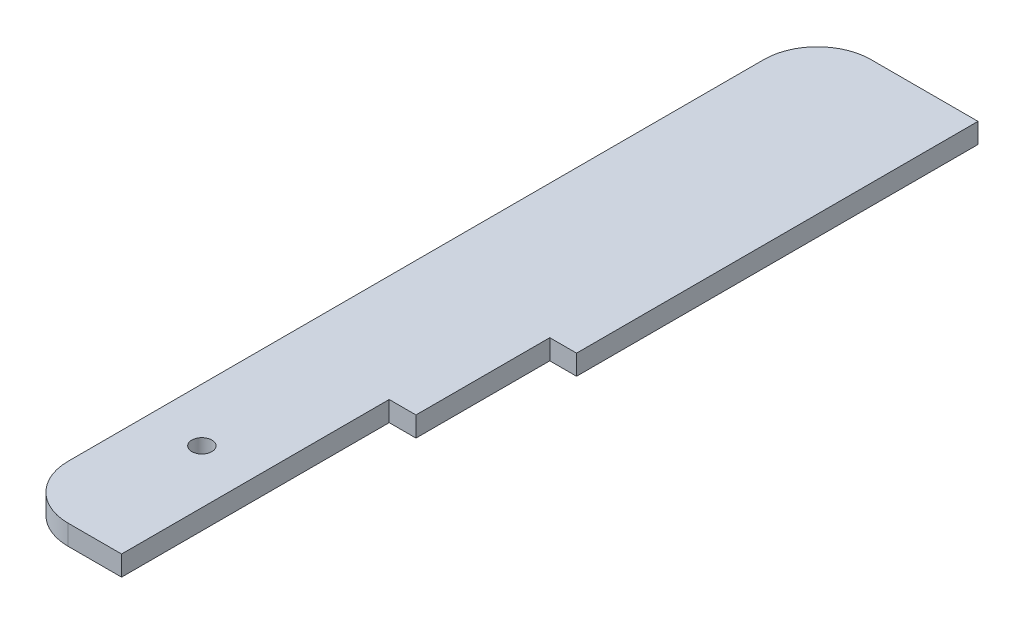
SolidWorks part; units mm, degrees
ref_plane "Front Plane" through (0, 0, 0) normal (0, 0, 1) x (1, 0, 0)
ref_plane "Top Plane" through (0, 0, 0) normal (0, 1, 0) x (1, 0, 0)
ref_plane "Right Plane" through (0, 0, 0) normal (1, 0, 0) x (0, 0, -1)
sketch "Sketch1" plane through (0, 0, 0) normal (0, 1, 0) x (1, 0, 0)
  line L0 (0, 0) -> (-50.8, 0)
  line L1 (0, 0) -> (0, 127)
  line L2 (0, 127) -> (12.7, 127)
  line L3 (12.7, 127) -> (12.7, 190.5)
  line L5 (-50.8, 381) -> (-50.8, 0)
  line L6 (12.7, 190.5) -> (25.4, 190.5)
  line L7 (25.4, 190.5) -> (25.4, 381)
  line L8 (25.4, 381) -> (-50.8, 381)
  dimension "D1" = 12.7
  dimension "D2" = 12.7
  dimension "D3" = 50.8
  dimension "D4" = 127
  dimension "D5" = 190.5
  dimension "D6" = 63.5
extrude "Boss-Extrude1" add sketch "Sketch1" along normal mid plane 9.525
fillet "Fillet1" radius 25.4 2 edges at (-50.8, 0, -381) (-50.8, 0, 0)
hole_wizard "3/8 (0.375) Diameter Hole1" positions "Sketch4" profile "Sketch3" hole size "3/8" standard "ANSI Inch"
sketch "Sketch4" plane through (0, 4.7625, 0) normal (0, 1, 0) x (1, 0, 0)
  line L0 (-25.4, 0) -> (0, 0) construction
  line L1 (0, 0) -> (0, 127) construction
  point P0 (-25.4, 63.5)
  dimension "D1" = 63.5
  dimension "D2" = 25.4
sketch "Sketch3" plane through (-25.4, 4.7625, -63.5) normal (1, 0, 0) x (0, 0, 1)
  line L0 (0, 0) -> (0, 14.5456)
  line L1 (0, 14.5456) -> (4.7625, 11.684)
  line L2 (4.7625, 11.684) -> (4.7625, 0)
  line L5 (4.7625, 0) -> (0, 0)
  line L10 (0, 14.5456) -> (-4.7625, 11.684) construction
  line L11 (0, -6.35) -> (0, 107.95) construction
  dimension "Hole Dia." = 9.525
  dimension "Hole Depth" = 11.684
  dimension "Drill Angle" = 118
